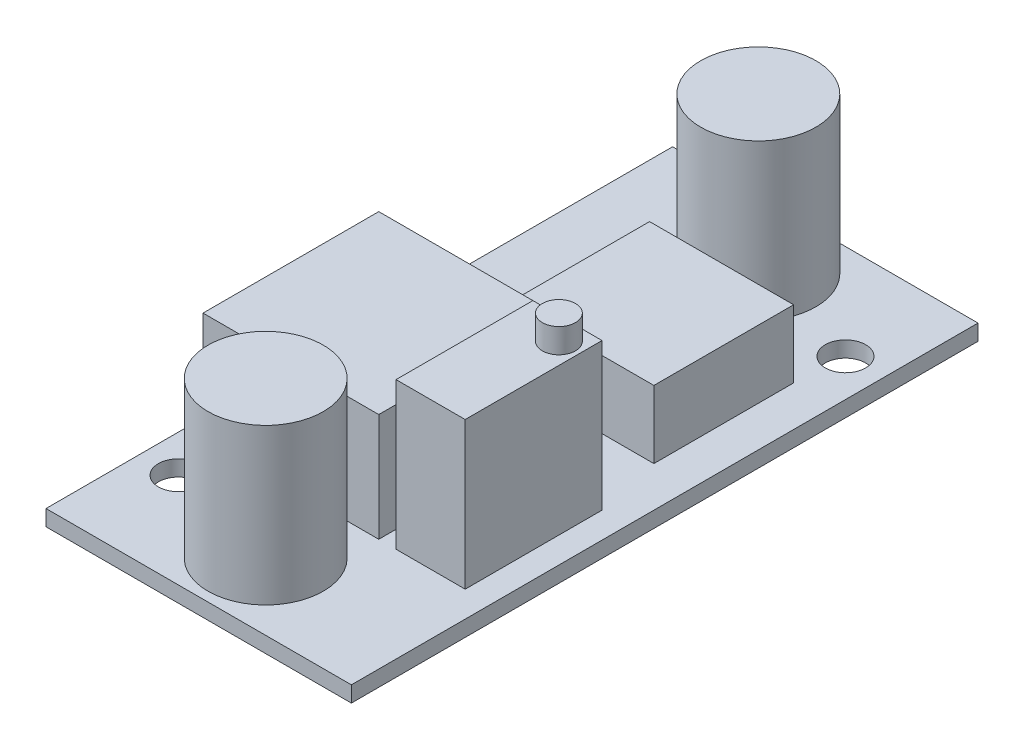
SolidWorks part; units mm, degrees
ref_plane "前视基准面" through (0, 0, 0) normal (0, 0, 1) x (1, 0, 0)
ref_plane "上视基准面" through (0, 0, 0) normal (0, 1, 0) x (1, 0, 0)
ref_plane "右视基准面" through (0, 0, 0) normal (1, 0, 0) x (0, 0, -1)
sketch "草图1" plane through (0, 0, 0) normal (0, 1, 0) x (1, 0, 0)
  line L1 (10.6, -21.75) -> (-10.6, -21.75)
  line L2 (10.6, -21.75) -> (10.6, 21.75)
  line L3 (10.6, 21.75) -> (-10.6, 21.75)
  line L4 (-10.6, -21.75) -> (-10.6, 21.75)
  line L5 (10.6, -21.75) -> (-10.6, 21.75) construction
  line L6 (10.6, 21.75) -> (-10.6, -21.75) construction
  circle A0 centre (8, 15.15) radius 1.4
  circle A1 centre (-8, -15.15) radius 1.4
  point P0 (0, 0)
  point P12 (0, 0)
  dimension "D3" = 2.8
  dimension "D1" = 21.2
  dimension "D2" = 43.5
  dimension "D4" = 6.6
  dimension "D5" = 2.6
  dimension "D6" = 2
extrude "凸台-拉伸1" add sketch "草图1" along normal blind 1.1
sketch "草图2" plane through (0, 1.1, 0) normal (0, 1, 0) x (1, 0, 0)
  circle A0 centre (0, 17.1) radius 4
  circle A1 centre (0, -17.1) radius 4
  point P7 (0, 0)
  dimension "D1" = 8
  dimension "D3" = 34.2
  dimension "D2" = 2
extrude "凸台-拉伸2" add sketch "草图2" along normal blind 10.8
sketch "草图3" plane through (0, 1.1, 0) normal (0, 1, 0) x (1, 0, 0)
  line L0 (-10.6, 21.75) -> (-10.6, -21.75) construction
  line L1 (-9.4, -12.05) -> (2.8, -12.05)
  line L2 (-9.4, -12.05) -> (-9.4, 0.15)
  line L3 (-9.4, 0.15) -> (2.8, 0.15)
  line L4 (2.8, -12.05) -> (2.8, 0.15)
  line L5 (-9.4, -12.05) -> (2.8, 0.15) construction
  line L6 (-9.4, 0.15) -> (2.8, -12.05) construction
  line L7 (-10.6, -21.75) -> (10.6, -21.75) construction
  point P0 (-3.3, -5.95)
  dimension "D1" = 12.2
  dimension "D2" = 1.2
  dimension "D3" = 9.7
extrude "凸台-拉伸3" add sketch "草图3" along normal blind 7.5
sketch "草图4" plane through (0, 1.1, 0) normal (0, 1, 0) x (1, 0, 0)
  line L0 (10.6, -21.75) -> (10.6, 21.75) construction
  line L1 (8.8, -2.55) -> (4, -2.55)
  line L2 (8.8, -2.55) -> (8.8, -12.05)
  line L3 (8.8, -12.05) -> (4, -12.05)
  line L4 (4, -2.55) -> (4, -12.05)
  line L5 (8.8, -2.55) -> (4, -12.05) construction
  line L6 (8.8, -12.05) -> (4, -2.55) construction
  line L7 (-10.6, -21.75) -> (10.6, -21.75) construction
  point P0 (6.4, -7.3)
  dimension "D1" = 4.8
  dimension "D2" = 9.5
  dimension "D3" = 1.8
  dimension "D4" = 9.7
extrude "凸台-拉伸4" add sketch "草图4" along normal blind 10.2
sketch "草图5" plane through (0, 1.1, 0) normal (0, 1, 0) x (1, 0, 0)
  line L0 (10.6, -21.75) -> (10.6, 21.75) construction
  line L1 (-2.2, 11.75) -> (7.8, 11.75)
  line L2 (-2.2, 11.75) -> (-2.2, 2.05)
  line L3 (-2.2, 2.05) -> (7.8, 2.05)
  line L4 (7.8, 11.75) -> (7.8, 2.05)
  line L5 (-2.2, 11.75) -> (7.8, 2.05) construction
  line L6 (-2.2, 2.05) -> (7.8, 11.75) construction
  line L7 (10.6, 21.75) -> (-10.6, 21.75) construction
  point P0 (2.8, 6.9)
  dimension "D1" = 9.7
  dimension "D2" = 10
  dimension "D3" = 2.8
  dimension "D4" = 10
extrude "凸台-拉伸5" add sketch "草图5" along normal blind 4.7
sketch "草图6" plane through (0, 11.3, 0) normal (0, 1, 0) x (1, 0, 0)
  circle A0 centre (7.3517, -4.096) radius 1.15
  dimension "D1" = 2.3
extrude "凸台-拉伸6" add sketch "草图6" along normal blind 1.7
